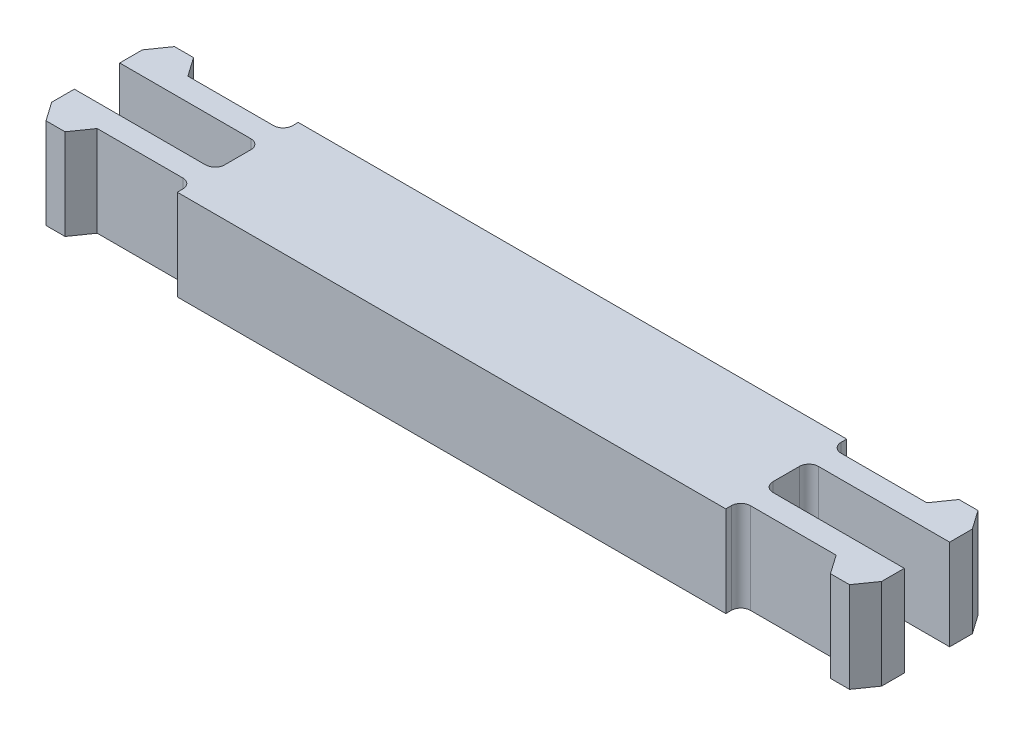
SolidWorks part; units mm, degrees
ref_plane "Front" through (0, 0, 0) normal (0, 0, 1) x (1, 0, 0)
ref_plane "Top" through (0, 0, 0) normal (0, 1, 0) x (1, 0, 0)
ref_plane "Right" through (0, 0, 0) normal (1, 0, 0) x (0, 0, -1)
sketch "Sketch1" plane through (0, 0, 0) normal (0, 1, 0) x (1, 0, 0)
  line L1 (-28.8, 6.35) -> (28.8, 6.35)
  line L2 (-28.8, 6.35) -> (-28.8, -6.35)
  line L3 (-28.8, -6.35) -> (28.8, -6.35)
  line L4 (28.8, 6.35) -> (28.8, -6.35)
  line L5 (-28.8, 6.35) -> (28.8, -6.35) construction
  line L6 (-28.8, -6.35) -> (28.8, 6.35) construction
  line L12 (-22.7682, 0) -> (21.9581, 0) construction
  line L13 (0, 9.9214) -> (0, -9.6014) construction
  point P0 (0, 0)
extrude "Boss-Extrude1" add sketch "Sketch1" along normal blind 9.525
sketch "Sketch2" plane through (0, 9.525, 0) normal (0, 1, 0) x (1, 0, 0)
  line L0 (-28.8, 4.7625) -> (-38.8, 4.7625)
  line L1 (-28.8, 6.35) -> (-28.8, -6.35) construction
  line L2 (-38.8, 4.7625) -> (-40.1895, 6.7469)
  line L3 (-40.1895, 6.7469) -> (-42.1895, 6.7469)
  line L4 (-42.1895, 6.7469) -> (-43.5789, 4.7625)
  line L5 (-43.5789, 4.7625) -> (-43.5789, 2.3812)
  line L6 (-43.5789, 2.3812) -> (-28.8, 2.3812)
  line L7 (-28.8, 2.3812) -> (-28.8, 4.7625)
  line L8 (28.8, 6.35) -> (-28.8, 6.35) construction
  dimension "D1" = 10
  dimension "D2" = 125
  dimension "D3" = 2.3813
  dimension "D4" = 1.5875
  dimension "D5" = 0.3969
  dimension "D6" = 2
extrude "Boss-Extrude2" add sketch "Sketch2" against normal up to surface (9.525 mm away) up to face at (0, 0, 0)
mirror "Mirror1" about plane through (0, 0, 0) normal (1, 0, 0) of "Boss-Extrude2"
mirror "Mirror2" about plane through (0, 0, 0) normal (0, 0, 1) of "Boss-Extrude2", "Mirror1"
fillet "Fillet1" radius 1 8 edges at (28.8, 4.7625, 4.7625) (28.8, 4.7625, 2.3812) (28.8, 4.7625, -2.3812) (28.8, 4.7625, -4.7625) (-28.8, 4.7625, 2.3812) (-28.8, 4.7625, 4.7625) (-28.8, 4.7625, -4.7625) (-28.8, 4.7625, -2.3812)
sketch "Sketch3" plane through (0, 0, -6.35) normal (0, 0, -1) x (-1, 0, 0)
  line L0 (28.8, 0) -> (28.8, 9.525) construction
  line L1 (-28.8, 0) -> (28.8, 0) construction
  circle A0 centre (24.257, 4.7625) radius 1.5875
  circle A1 centre (-24.257, 4.7625) radius 1.5875
  point P4 (28.8, 4.7625)
  point P10 (0, 0)
  dimension "D1" = 3.175
  dimension "D3" = 48.514
  dimension "D2" = 24.257
extrude "Boss-Extrude3" [suppressed] add sketch "Sketch3" along normal blind 6.35
mirror "Mirror5" [suppressed] about plane through (0, 0, 0) normal (0, 0, 1)
